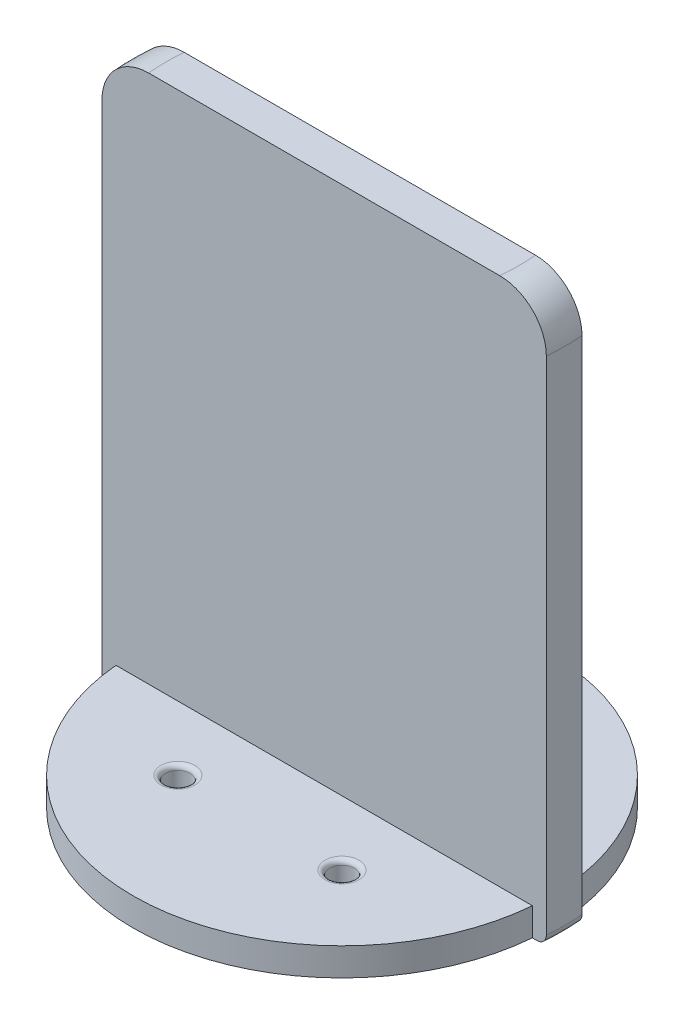
SolidWorks part; units mm, degrees
ref_plane "前视基准面" through (0, 0, 0) normal (0, 0, 1) x (1, 0, 0)
ref_plane "上视基准面" through (0, 0, 0) normal (0, 1, 0) x (1, 0, 0)
ref_plane "右视基准面" through (0, 0, 0) normal (1, 0, 0) x (0, 0, -1)
other "Configuration Table"
sketch "草图1" plane through (0, 0, 0) normal (0, 1, 0) x (1, 0, 0)
  circle A0 centre (8.8388, 8.8388) radius 1.3333
  circle A1 centre (8.8388, -8.8388) radius 1.3333
  circle A2 centre (-8.8388, -8.8388) radius 1.3333
  circle A3 centre (-8.8388, 8.8388) radius 1.3333
  circle A4 centre (0, 0) radius 22.5
  point P13 (0, 0)
  dimension "D1" = 4
  dimension "D3" = 45
  dimension "D2" = 12.5
extrude "凸台-拉伸1" add sketch "草图1" along normal blind 3
sketch "草图3" plane through (0, 0, 0) normal (0, -1, 0) x (1, 0, 0)
  line L1 (-23.9231, 1.92) -> (23.9231, 1.92)
  line L3 (23.9231, -1.92) -> (-23.9231, -1.92)
  arc A0 (-23.9231, 1.92) -> (-23.9231, -1.92) centre (0, 0) ccw
  arc A1 (23.9231, -1.92) -> (23.9231, 1.92) centre (0, 0) ccw
extrude "凸台-拉伸2" add sketch "草图3" against normal blind 60
fillet "圆角1" radius 0.5 4 edges at (-8.8388, 3, -7.5055) (-8.8388, 3, 10.1722) (8.8388, 3, 10.1722) (8.8388, 3, -7.5055)
fillet "圆角2" radius 1 2 edges at (-24, 0, 0) (24, 0, 0)
fillet "圆角3" radius 5 2 edges at (24, 60, 0) (-24, 60, 0)
